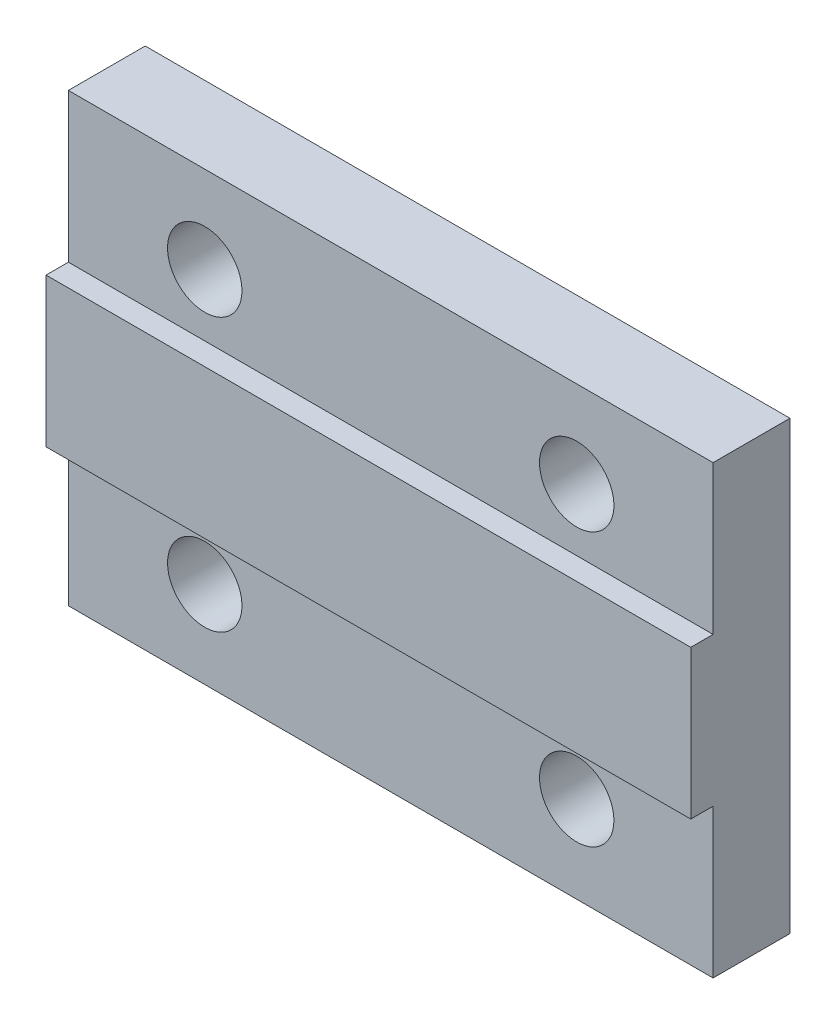
SolidWorks part; units mm, degrees
ref_plane "前视基准面" through (0, 0, 0) normal (0, 0, 1) x (1, 0, 0)
ref_plane "上视基准面" through (0, 0, 0) normal (0, 1, 0) x (1, 0, 0)
ref_plane "右视基准面" through (0, 0, 0) normal (1, 0, 0) x (0, 0, -1)
sketch "草图1" plane through (0, 0, 0) normal (0, 0, 1) x (1, 0, 0)
  line L1 (0, 0) -> (26, 0)
  line L2 (0, 0) -> (0, 18)
  line L3 (0, 18) -> (26, 18)
  line L4 (26, 0) -> (26, 18)
  dimension "D1" = 26
  dimension "D2" = 18
extrude "凸台-拉伸1" add sketch "草图1" along normal blind 4
sketch "草图2" plane through (26, 0, 0) normal (1, 0, 0) x (0, 0, -1)
  line L0 (-4, 9) -> (1.7713, 9) construction
  line L1 (-4, 0) -> (-4, 18) construction
  line L2 (-4, 6) -> (-3.1, 6)
  line L3 (-4, 18) -> (-3.1, 18)
  line L4 (-4, 18) -> (-4, 12)
  line L5 (-4, 12) -> (-3.1, 12)
  line L6 (-3.1, 18) -> (-3.1, 12)
  line L7 (-4, 0) -> (-4, 6)
  line L8 (-3.1, 0) -> (-3.1, 6)
  line L9 (-4, 0) -> (-3.1, 0)
  dimension "D1" = 0.9
  dimension "D2" = 6
extrude "切除-拉伸1" cut sketch "草图2" against normal through all
sketch "草图3" plane through (0, 0, 3.1) normal (0, 0, 1) x (1, 0, 0)
  line L0 (13, 18) -> (13, 0) construction
  line L1 (0, 18) -> (26, 18) construction
  line L2 (0, 0) -> (26, 0) construction
  line L3 (13, 0) -> (13, 9) construction
  line L4 (13, 9) -> (27.5646, 9) construction
  circle A0 centre (5.5, 14.5) radius 1.5
  circle A1 centre (5.5, 3.5) radius 1.5
  circle A2 centre (20.5, 3.5) radius 1.5
  circle A3 centre (20.5, 14.5) radius 1.5
  dimension "D3" = 3
  dimension "D1" = 11
  dimension "D2" = 15
extrude "切除-拉伸2" cut sketch "草图3" against normal blind 4
